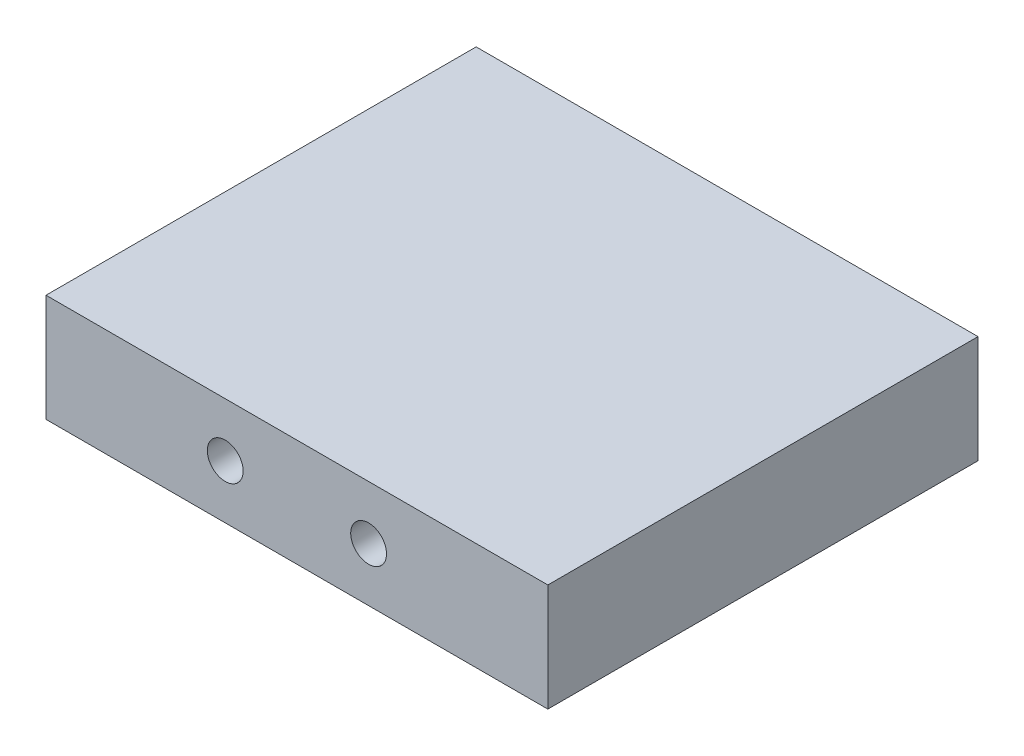
SolidWorks part; units mm, degrees
material "Oak"
ref_plane "Front Plane" through (0, 0, 0) normal (0, 0, 1) x (1, 0, 0)
ref_plane "Top Plane" through (0, 0, 0) normal (0, 1, 0) x (1, 0, 0)
ref_plane "Right Plane" through (0, 0, 0) normal (1, 0, 0) x (0, 0, -1)
other "Configuration Table"
sketch "Sketch1" plane through (0, 0, 0) normal (0, 1, 0) x (1, 0, 0)
  line L1 (-44.45, 38.1) -> (44.45, 38.1)
  line L2 (-44.45, 38.1) -> (-44.45, -38.1)
  line L3 (-44.45, -38.1) -> (44.45, -38.1)
  line L4 (44.45, 38.1) -> (44.45, -38.1)
  line L5 (-44.45, 38.1) -> (44.45, -38.1) construction
  line L6 (-44.45, -38.1) -> (44.45, 38.1) construction
  point P0 (0, 0)
  dimension "D1" = 88.9
  dimension "D2" = 76.2
extrude "Boss-Extrude1" add sketch "Sketch1" along normal blind 19.05
sketch "Sketch2" plane through (0, 0, 38.1) normal (0, 0, 1) x (1, 0, 0)
  line L0 (44.45, 19.05) -> (44.45, 0) construction
  line L1 (-44.45, 19.05) -> (-44.45, 0) construction
  line L2 (-44.45, 19.05) -> (44.45, 19.05) construction
  circle A0 centre (-12.7, 9.525) radius 3.175
  circle A1 centre (12.7, 9.525) radius 3.175
  dimension "D1" = 6.35
  dimension "D2" = 6.35
  dimension "D3" = 31.75
  dimension "D4" = 31.75
  dimension "D6" = 9.525
extrude "Cut-Extrude1" cut sketch "Sketch2" against normal blind 12.7
